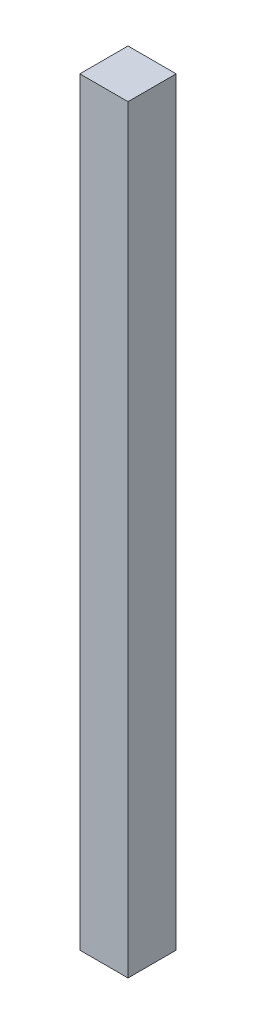
SolidWorks part; units mm, degrees
ref_plane "Front Plane" through (0, 0, 0) normal (0, 0, 1) x (1, 0, 0)
ref_plane "Top Plane" through (0, 0, 0) normal (0, 1, 0) x (1, 0, 0)
ref_plane "Right Plane" through (0, 0, 0) normal (1, 0, 0) x (0, 0, -1)
sketch "Sketch1" plane through (0, 0, 0) normal (0, 1, 0) x (1, 0, 0)
  line L1 (-39.8355, 18.6136) -> (-14.4355, 18.6136)
  line L2 (-39.8355, 18.6136) -> (-39.8355, -6.7864)
  line L3 (-39.8355, -6.7864) -> (-14.4355, -6.7864)
  line L4 (-14.4355, 18.6136) -> (-14.4355, -6.7864)
  dimension "D1" = 25.4
  dimension "D2" = 25.4
extrude "Boss-Extrude1" add sketch "Sketch1" along normal blind 400
